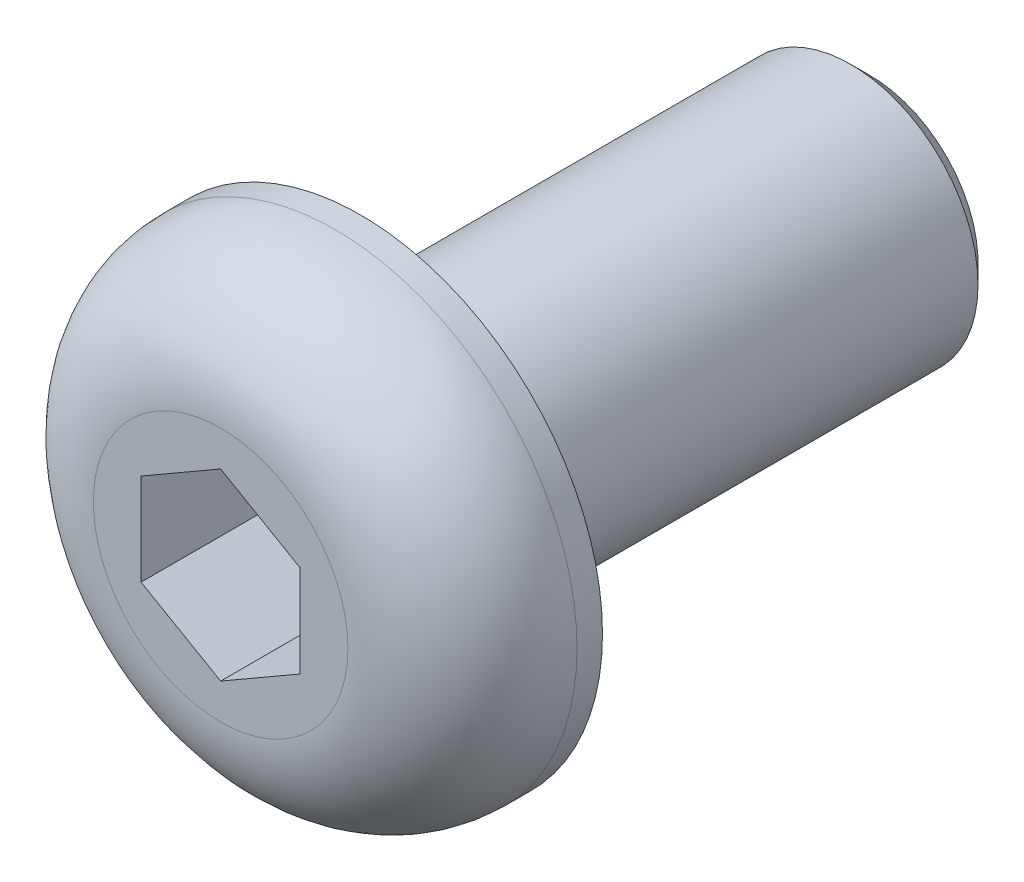
SolidWorks part; units mm, degrees
ref_plane "Front Plane" through (0, 0, 0) normal (0, 0, 1) x (1, 0, 0)
ref_plane "Top Plane" through (0, 0, 0) normal (0, 1, 0) x (1, 0, 0)
ref_plane "Right Plane" through (0, 0, 0) normal (1, 0, 0) x (0, 0, -1)
sketch "Sketch1" plane through (0, 0, 0) normal (0, 0, 1) x (1, 0, 0)
  circle A0 centre (0, 0) radius 3.8
  dimension "D1" = 7.6
extrude "Boss-Extrude1" add sketch "Sketch1" along normal blind 2.2
sketch "Sketch2" plane through (0, 0, 0) normal (0, 0, -1) x (-1, 0, 0)
  circle A0 centre (0, 0) radius 2
  dimension "D1" = 4
extrude "Boss-Extrude2" add sketch "Sketch2" along normal blind 8
chamfer "Chamfer1" distance 0.3 angle 45 1 edges at (-2, 0, -8)
sketch "Sketch3" plane through (0, 0, 2.2) normal (0, 0, 1) x (1, 0, 0)
  line L1 (0, 1.4434) -> (-1.25, 0.7217)
  line L2 (-1.25, 0.7217) -> (-1.25, -0.7217)
  line L3 (-1.25, -0.7217) -> (0, -1.4434)
  line L4 (0, -1.4434) -> (1.25, -0.7217)
  line L5 (1.25, -0.7217) -> (1.25, 0.7217)
  line L6 (1.25, 0.7217) -> (0, 1.4434)
  circle A0 centre (0, 0) radius 1.25 construction
  dimension "D1" = 2.5
extrude "Cut-Extrude1" cut sketch "Sketch3" against normal blind 2
fillet "Fillet1" radius 1.8 1 edges at (3.8, 0, 2.2)
